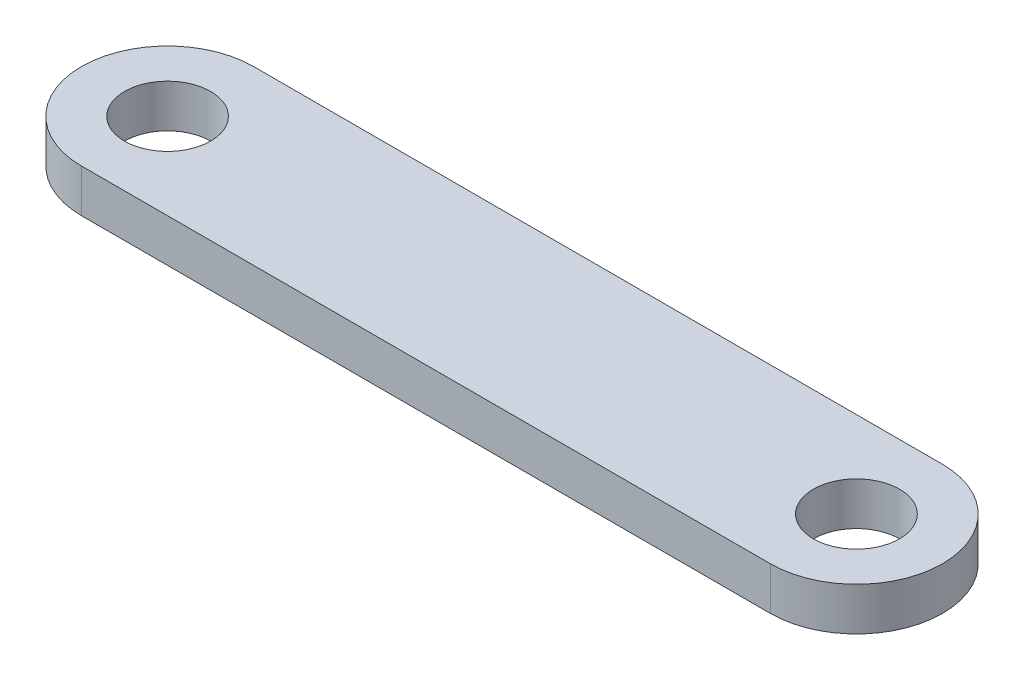
SolidWorks part; units mm, degrees
ref_plane "Front Plane" through (0, 0, 0) normal (0, 0, 1) x (1, 0, 0)
ref_plane "Top Plane" through (0, 0, 0) normal (0, 1, 0) x (1, 0, 0)
ref_plane "Right Plane" through (0, 0, 0) normal (1, 0, 0) x (0, 0, -1)
sketch "Sketch2" plane through (0, 0, 0) normal (0, 1, 0) x (1, 0, 0)
  line L0 (-16, 0) -> (16, 0) construction
  line L1 (-16, 4) -> (16, 4)
  line L2 (-16, -4) -> (16, -4)
  arc A0 (-16, 4) -> (-16, -4) centre (-16, 0) ccw
  arc A1 (16, -4) -> (16, 4) centre (16, 0) ccw
  circle A2 centre (16, 0) radius 2
  circle A3 centre (-16, 0) radius 2
  point P2 (0, 0)
  dimension "D2" = 4
  dimension "D3" = 4
  dimension "D4" = 4
  dimension "D1" = 32
extrude "Boss-Extrude1" add sketch "Sketch2" along normal mid plane 2
